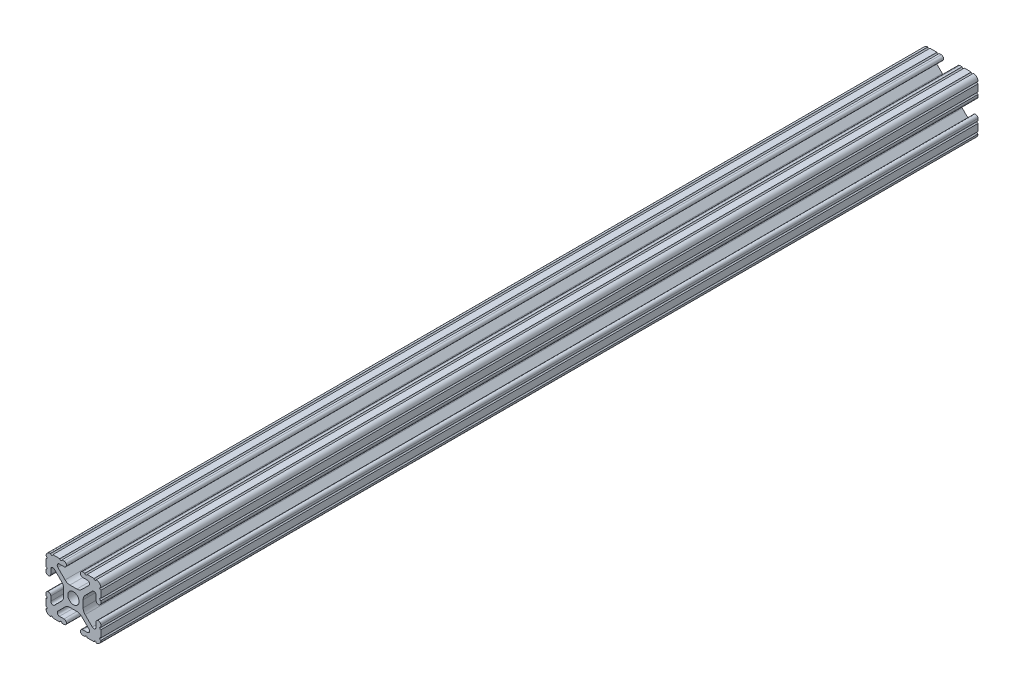
SolidWorks part; units mm, degrees
ref_plane "Front Plane" through (0, 0, 0) normal (0, 0, 1) x (1, 0, 0)
ref_plane "Top Plane" through (0, 0, 0) normal (0, 1, 0) x (1, 0, 0)
ref_plane "Right Plane" through (0, 0, 0) normal (1, 0, 0) x (0, 0, -1)
ref_plane "Plane1" through (0, 0, -450.85) normal (0, 0, -1) x (-1, 0, 0)
sketch "Sketch1" plane through (0, 0, -450.85) normal (0, 0, -1) x (-1, 0, 0)
  line L0 (12.7, -9.5504) -> (12.7, -6.3331)
  line L1 (12.7, -5.3171) -> (12.7, -4.3434)
  line L2 (10.4902, -4.3434) -> (10.4902, -6.4748)
  line L3 (8.7558, -7.1932) -> (5.4257, -3.8632)
  line L4 (4.4958, -1.6181) -> (4.4958, 1.6181)
  line L5 (5.4257, 3.8632) -> (8.7558, 7.1932)
  line L6 (10.4902, 6.4748) -> (10.4902, 4.3434)
  line L7 (12.7, 4.3434) -> (12.7, 5.3171)
  line L8 (12.7, 6.3331) -> (12.7, 9.5504)
  line L9 (9.5504, 12.7) -> (6.3331, 12.7)
  line L10 (5.3171, 12.7) -> (4.3434, 12.7)
  line L11 (4.3434, 10.4902) -> (6.4748, 10.4902)
  line L12 (7.1932, 8.7558) -> (3.8632, 5.4257)
  line L13 (1.6181, 4.4958) -> (-1.6181, 4.4958)
  line L14 (-3.8632, 5.4257) -> (-7.1932, 8.7558)
  line L15 (-6.4748, 10.4902) -> (-4.3434, 10.4902)
  line L16 (-4.3434, 12.7) -> (-5.3171, 12.7)
  line L17 (-6.3331, 12.7) -> (-9.5504, 12.7)
  line L18 (-12.7, 9.5504) -> (-12.7, 6.3331)
  line L19 (-12.7, 5.3171) -> (-12.7, 4.3434)
  line L20 (-10.4902, 4.3434) -> (-10.4902, 6.4748)
  line L21 (-8.7558, 7.1932) -> (-5.4257, 3.8632)
  line L22 (-4.4958, 1.6181) -> (-4.4958, -1.6181)
  line L23 (-5.4257, -3.8632) -> (-8.7558, -7.1932)
  line L24 (-10.4902, -6.4748) -> (-10.4902, -4.3434)
  line L25 (-12.7, -4.3434) -> (-12.7, -5.3171)
  line L26 (-12.7, -6.3331) -> (-12.7, -9.5504)
  line L27 (-9.5504, -12.7) -> (-6.3331, -12.7)
  line L28 (-5.3171, -12.7) -> (-4.3434, -12.7)
  line L29 (-4.3434, -10.4902) -> (-6.4748, -10.4902)
  line L30 (-7.1932, -8.7558) -> (-3.8632, -5.4257)
  line L31 (-1.6181, -4.4958) -> (1.6181, -4.4958)
  line L32 (3.8632, -5.4257) -> (7.1932, -8.7558)
  line L33 (6.4748, -10.4902) -> (4.3434, -10.4902)
  line L34 (4.3434, -12.7) -> (5.3171, -12.7)
  line L35 (6.3331, -12.7) -> (9.5504, -12.7)
  arc A0 (12.6998, -10.5664) -> (12.7, -9.5504) centre (12.7, -10.0584) cw
  arc A1 (12.7, -6.3331) -> (12.7, -5.3171) centre (12.7, -5.8251) cw
  arc A2 (12.7, -4.3434) -> (10.4902, -4.3434) centre (11.5951, -4.3434) ccw
  arc A3 (10.4902, -6.4748) -> (8.7558, -7.1932) centre (9.4742, -6.4748) cw
  arc A4 (5.4257, -3.8632) -> (4.4958, -1.6181) centre (7.6708, -1.6181) cw
  arc A5 (4.4958, 1.6181) -> (5.4257, 3.8632) centre (7.6708, 1.6181) cw
  arc A6 (8.7558, 7.1932) -> (10.4902, 6.4748) centre (9.4742, 6.4748) cw
  arc A7 (10.4902, 4.3434) -> (12.7, 4.3434) centre (11.5951, 4.3434) ccw
  arc A8 (12.7, 5.3171) -> (12.7, 6.3331) centre (12.7, 5.8251) cw
  arc A9 (12.7, 9.5504) -> (12.6998, 10.5664) centre (12.7, 10.0584) cw
  arc A10 (12.6998, 10.5664) -> (10.5664, 12.6998) centre (10.5918, 10.5918) ccw
  arc A11 (10.5664, 12.6998) -> (9.5504, 12.7) centre (10.0584, 12.7) cw
  arc A12 (6.3331, 12.7) -> (5.3171, 12.7) centre (5.8251, 12.7) cw
  arc A13 (4.3434, 12.7) -> (4.3434, 10.4902) centre (4.3434, 11.5951) ccw
  arc A14 (6.4748, 10.4902) -> (7.1932, 8.7558) centre (6.4748, 9.4742) cw
  arc A15 (3.8632, 5.4257) -> (1.6181, 4.4958) centre (1.6181, 7.6708) cw
  arc A16 (-1.6181, 4.4958) -> (-3.8632, 5.4257) centre (-1.6181, 7.6708) cw
  arc A17 (-7.1932, 8.7558) -> (-6.4748, 10.4902) centre (-6.4748, 9.4742) cw
  arc A18 (-4.3434, 10.4902) -> (-4.3434, 12.7) centre (-4.3434, 11.5951) ccw
  arc A19 (-5.3171, 12.7) -> (-6.3331, 12.7) centre (-5.8251, 12.7) cw
  arc A20 (-9.5504, 12.7) -> (-10.5664, 12.6998) centre (-10.0584, 12.7) cw
  arc A21 (-10.5664, 12.6998) -> (-12.6998, 10.5664) centre (-10.5918, 10.5918) ccw
  arc A22 (-12.6998, 10.5664) -> (-12.7, 9.5504) centre (-12.7, 10.0584) cw
  arc A23 (-12.7, 6.3331) -> (-12.7, 5.3171) centre (-12.7, 5.8251) cw
  arc A24 (-12.7, 4.3434) -> (-10.4902, 4.3434) centre (-11.5951, 4.3434) ccw
  arc A25 (-10.4902, 6.4748) -> (-8.7558, 7.1932) centre (-9.4742, 6.4748) cw
  arc A26 (-5.4257, 3.8632) -> (-4.4958, 1.6181) centre (-7.6708, 1.6181) cw
  arc A27 (-4.4958, -1.6181) -> (-5.4257, -3.8632) centre (-7.6708, -1.6181) cw
  arc A28 (-8.7558, -7.1932) -> (-10.4902, -6.4748) centre (-9.4742, -6.4748) cw
  arc A29 (-10.4902, -4.3434) -> (-12.7, -4.3434) centre (-11.5951, -4.3434) ccw
  arc A30 (-12.7, -5.3171) -> (-12.7, -6.3331) centre (-12.7, -5.8251) cw
  arc A31 (-12.7, -9.5504) -> (-12.6998, -10.5664) centre (-12.7, -10.0584) cw
  arc A32 (-12.6998, -10.5664) -> (-10.5664, -12.6998) centre (-10.5918, -10.5918) ccw
  arc A33 (-10.5664, -12.6998) -> (-9.5504, -12.7) centre (-10.0584, -12.7) cw
  arc A34 (-6.3331, -12.7) -> (-5.3171, -12.7) centre (-5.8251, -12.7) cw
  arc A35 (-4.3434, -12.7) -> (-4.3434, -10.4902) centre (-4.3434, -11.5951) ccw
  arc A36 (-6.4748, -10.4902) -> (-7.1932, -8.7558) centre (-6.4748, -9.4742) cw
  arc A37 (-3.8632, -5.4257) -> (-1.6181, -4.4958) centre (-1.6181, -7.6708) cw
  arc A38 (1.6181, -4.4958) -> (3.8632, -5.4257) centre (1.6181, -7.6708) cw
  arc A39 (7.1932, -8.7558) -> (6.4748, -10.4902) centre (6.4748, -9.4742) cw
  arc A40 (4.3434, -10.4902) -> (4.3434, -12.7) centre (4.3434, -11.5951) ccw
  arc A41 (5.3171, -12.7) -> (6.3331, -12.7) centre (5.8251, -12.7) cw
  arc A42 (9.5504, -12.7) -> (10.5664, -12.6998) centre (10.0584, -12.7) cw
  arc A43 (10.5664, -12.6998) -> (12.6998, -10.5664) centre (10.5918, -10.5918) ccw
  circle A44 centre (0, 0) radius 2.6035
extrude "Boss-Extrude1" add sketch "Sketch1" against normal blind 406.4
